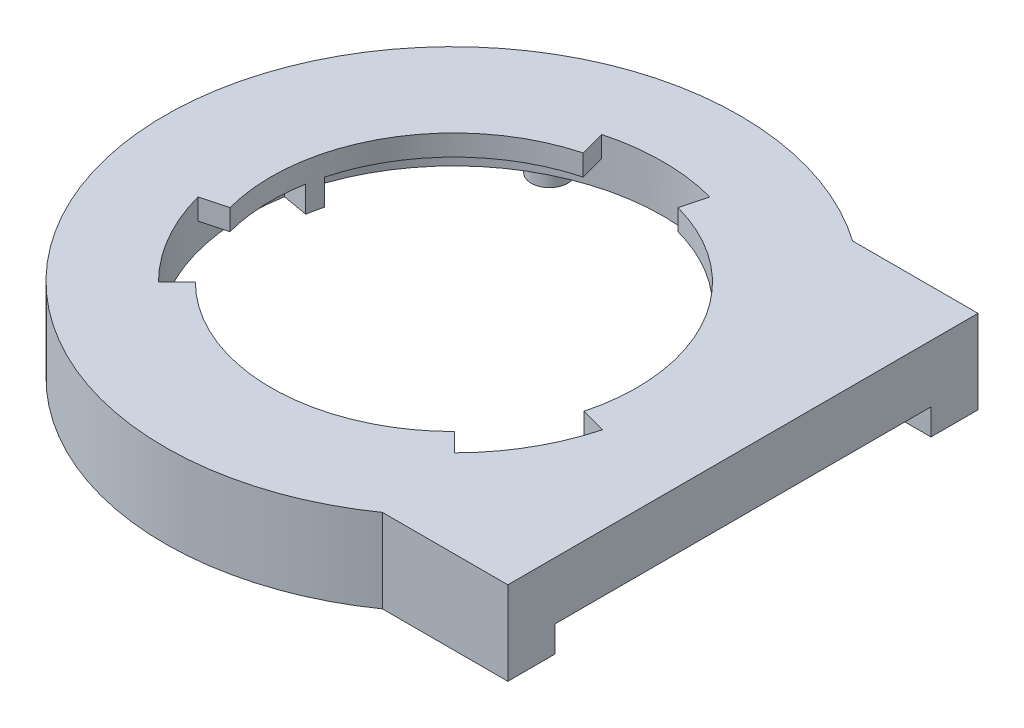
SolidWorks part; units mm, degrees
material "Melamine resin"
ref_plane "Front Plane" through (0, 0, 0) normal (0, 0, 1) x (1, 0, 0)
ref_plane "Top Plane" through (0, 0, 0) normal (0, 1, 0) x (1, 0, 0)
ref_plane "Right Plane" through (0, 0, 0) normal (1, 0, 0) x (0, 0, -1)
sketch "Sketch1" plane through (0, 0, 0) normal (0, 1, 0) x (1, 0, 0)
  line L0 (24.6843, 44.9998) -> (55.3157, 44.9998)
  line L1 (24.6843, 44.9998) -> (24.6843, -45.0002)
  line L2 (24.6843, -45.0002) -> (55.3157, -45.0002)
  line L3 (55.3157, 44.9998) -> (55.3157, -45.0002)
  circle A0 centre (-0.3157, 0) radius 55
extrude "Boss-Extrude1" add sketch "Sketch1" along normal blind 16 contours L0 A0 L2 L1 | A0 L2 L3 L0 | L2 A0 L0 L1
sketch "Sketch3" plane through (0, 0, 0) normal (0, -1, 0) x (1, 0, 0)
  line L0 (31.3068, 45.0002) -> (55.3157, 45.0002) construction
  line L1 (50.3157, 40.2002) -> (13.6488, 40.2002)
  line L2 (50.3157, 40.2002) -> (50.3157, -40.1998)
  line L3 (50.3157, -40.1998) -> (13.6488, -40.1998)
  line L4 (13.6488, 40.2002) -> (13.6488, -40.1998)
  line L5 (31.3073, -44.9998) -> (55.3157, -44.9998) construction
  line L6 (55.3157, -44.9998) -> (55.3157, 45.0002) construction
  circle A0 centre (0, 0) radius 50
  dimension "D1" = 100
  dimension "D2" = 4.8
  dimension "D3" = 4.8
  dimension "D4" = 5
extrude "Cut-Extrude1" cut sketch "Sketch3" against normal blind 12 contours L1 A0 L3 L4 | L3 A0 L1 L4 | A0 L3 L2 L1
sketch "Sketch4" plane through (55.3157, 0, 0) normal (1, 0, 0) x (0, 0, -1)
  line L0 (44.9998, 0) -> (-45.0002, 0) construction
  line L1 (-36.0002, 5) -> (35.9998, 5)
  line L2 (-36.0002, 5) -> (-36.0002, 0)
  line L3 (-36.0002, 0) -> (35.9998, 0)
  line L4 (35.9998, 5) -> (35.9998, 0)
  line L5 (-45.0002, 16) -> (-45.0002, 0) construction
  dimension "D1" = 72
  dimension "D2" = 5
  dimension "D3" = 9
extrude "Cut-Extrude2" cut sketch "Sketch4" against normal blind 16
sketch "Sketch5" plane through (0, 16, 0) normal (0, 1, 0) x (1, 0, 0)
  circle A0 centre (0, 0) radius 35
  dimension "D1" = 70
extrude "Cut-Extrude3" cut sketch "Sketch5" against normal blind 16
sketch "Sketch6" plane through (0, 16, 0) normal (0, 1, 0) x (1, 0, 0)
  line L7 (-24.7487, -24.7487) -> (-28.2843, -28.2843)
  line L8 (-33.8074, -9.0587) -> (-38.637, -10.3528)
  line L9 (24.8135, -24.6838) -> (28.3583, -28.2101)
  line L10 (33.831, -8.9701) -> (38.664, -10.2515)
  line L11 (-9.0587, 33.8074) -> (-10.3528, 38.637)
  line L12 (9.0587, 33.8074) -> (10.3528, 38.637)
  line L13 (-34.641, -20) -> (-30.3109, -17.5)
  line L14 (34.6933, -19.9092) -> (30.3566, -17.4205)
  arc A0 (-38.637, -10.3528) -> (-28.2843, -28.2843) centre (0, 0) ccw
  arc A1 (-33.8074, -9.0587) -> (-24.7487, -24.7487) centre (0, 0) ccw
  arc A3 (9.0587, 33.8074) -> (-9.0587, 33.8074) centre (0, 0) ccw
  arc A4 (10.3528, 38.637) -> (-10.3528, 38.637) centre (0, 0) ccw
  arc A5 (24.8135, -24.6838) -> (33.831, -8.9701) centre (0, 0) ccw
  arc A6 (28.3583, -28.2101) -> (38.664, -10.2515) centre (0, 0) ccw
  circle M1 centre (0, 0) radius 35
  dimension "D1" = 80
  dimension "D2" = 5
  dimension "D3" = 5
  dimension "D4" = 15
  dimension "D5" = 165
  dimension "D6" = 15
  dimension "D7" = 165
extrude "Cut-Extrude4" cut sketch "Sketch6" against normal blind 10 contours L13 A0 L7 M1 | L8 A0 L13 M1 | L12 A4 L11 M1 | L14 A6 L10 M1 | L9 A6 L14 M1
sketch "Sketch7" plane through (0, 12, 0) normal (0, -1, 0) x (1, 0, 0)
  line L11 (10.3528, 38.637) -> (9.0587, 33.8074)
  line L12 (13.6808, 37.5877) -> (11.9707, 32.8892)
  line L14 (28.2843, -28.2843) -> (24.7487, -24.7487)
  line L15 (25.7115, -30.6418) -> (22.4976, -26.8116)
  line L17 (-38.637, -10.3528) -> (-33.8074, -9.0587)
  line L18 (-39.3923, -6.9459) -> (-34.4683, -6.0777)
  circle A0 centre (0, 0) radius 42
  arc A1 (28.2843, -28.2843) -> (13.6808, 37.5877) centre (0, 0) ccw
  circle A3 centre (0, 0) radius 35
  arc A5 (-38.637, -10.3528) -> (25.7115, -30.6418) centre (0, 0) ccw
  arc A6 (10.3528, 38.637) -> (-39.3923, -6.9459) centre (0, 0) ccw
  point P7 (36.3958, -20.9606)
  point P43 (-36.3303, -21.0739)
  arc M5 (-38.637, 10.3528) -> (-28.2843, 28.2843) centre (0, 0) cw
  arc M7 (-24.7487, 24.7487) -> (24.8135, 24.6838) centre (0, 0) cw
  arc M9 (28.3583, 28.2101) -> (38.664, 10.2515) centre (0, 0) cw
  arc M11 (33.831, 8.9701) -> (9.0587, -33.8074) centre (0, 0) cw
  arc M13 (10.3528, -38.637) -> (-10.3528, -38.637) centre (0, 0) cw
  arc M15 (-9.0587, -33.8074) -> (-33.8074, 9.0587) centre (0, 0) cw
  dimension "D1" = 84
  dimension "D2" = 80
  dimension "D3" = 70
  dimension "D10" = 5
  dimension "D11" = 5
  dimension "D12" = 5
extrude "Boss-Extrude2" add sketch "Sketch7" along normal blind 5 contours A0 A6 L11 L12 A1 L14 L15 A5 L17 L18 M7 M9 M11 M13 M15 M5
sketch "Sketch8" plane through (0, 12, 0) normal (0, -1, 0) x (1, 0, 0)
  line L8 (50.3157, 40.2002) -> (29.7312, 40.2002) construction
  line L10 (50.3157, -40.1998) -> (29.7317, -40.1998) construction
  circle A1 centre (31.3068, 40.2002) radius 1.5
  arc A3 (29.7312, 40.2002) -> (29.7317, -40.1998) centre (0, 0) ccw construction
  circle A4 centre (-25, 43.3013) radius 3.5
  circle A5 centre (-25, -43.3013) radius 3.5
  circle A6 centre (31.3068, 40.2002) radius 3.5
  circle A7 centre (31.3073, -40.1998) radius 3.5
  circle A8 centre (-25, 43.3013) radius 1.5
  circle A9 centre (-25, -43.3013) radius 1.5
  circle A10 centre (31.3073, -40.1998) radius 1.5
  dimension "D1" = 3
  dimension "D2" = 7
  dimension "D3" = 7
  dimension "D4" = 7
  dimension "D5" = 7
  dimension "D6" = 3
  dimension "D7" = 3
  dimension "D8" = 3
extrude "Boss-Extrude3" add sketch "Sketch8" along normal blind 12
sketch "Sketch9" plane through (0, 12, 0) normal (0, -1, 0) x (1, 0, 0)
  line L0 (32.8068, 40.2002) -> (29.8068, 40.2002) construction
  line L1 (32.8073, -40.1998) -> (29.8073, -40.1998) construction
  circle A0 centre (-25, 43.3013) radius 1.5
  arc A1 (-23.6899, 44.0317) -> (-26.2876, 42.5319) centre (0, 0) ccw construction
  circle A2 centre (31.3068, 40.2002) radius 1.5
  circle A3 centre (-25, -43.3013) radius 1.5
  arc A4 (-26.2876, -42.5319) -> (-23.6899, -44.0317) centre (0, 0) ccw construction
  circle A5 centre (31.3073, -40.1998) radius 1.5
extrude "Cut-Extrude5" cut sketch "Sketch9" along normal blind 12
